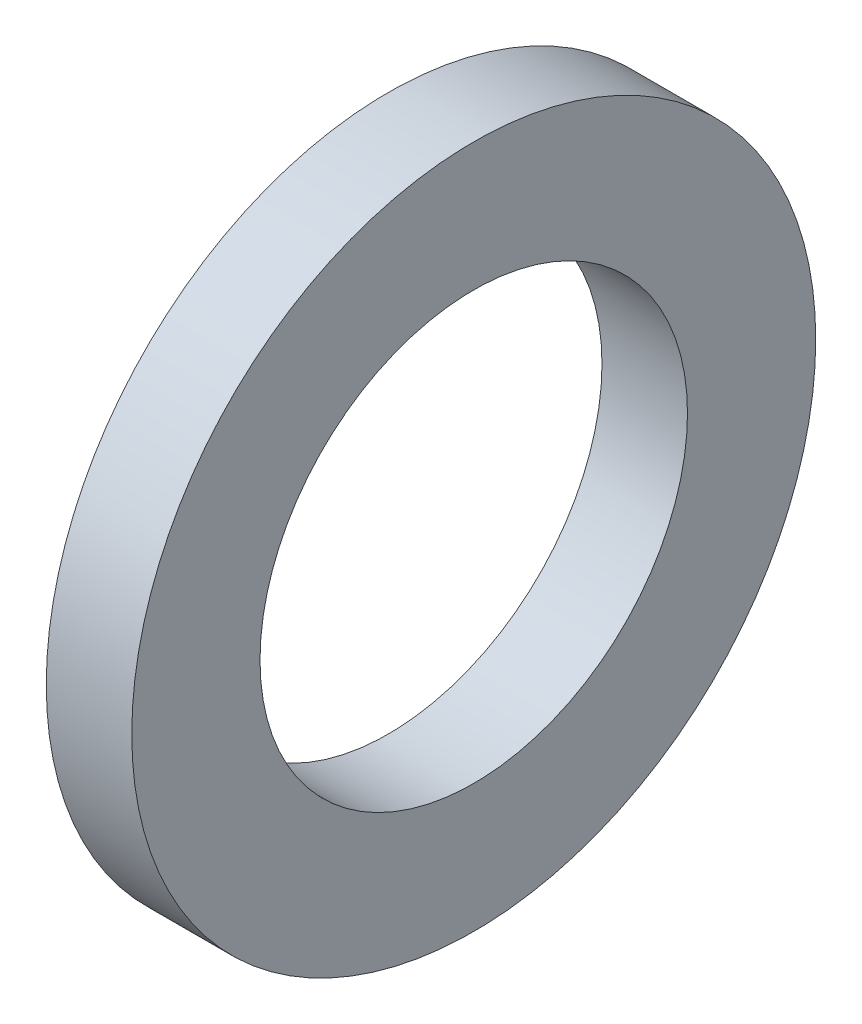
SolidWorks part; units mm, degrees
ref_plane "Front Plane" through (0, 0, 0) normal (0, 0, 1) x (1, 0, 0)
ref_plane "Top Plane" through (0, 0, 0) normal (0, 1, 0) x (1, 0, 0)
ref_plane "Right Plane" through (0, 0, 0) normal (1, 0, 0) x (0, 0, -1)
sketch "Sketch1" plane through (0, 0, 0) normal (1, 0, 0) x (0, 0, -1)
  circle A0 centre (0, 0) radius 2.5
  circle A1 centre (0, 0) radius 4
  dimension "D1" = 8
  dimension "D2" = 5
extrude "Boss-Extrude1" add sketch "Sketch1" along normal blind 1
